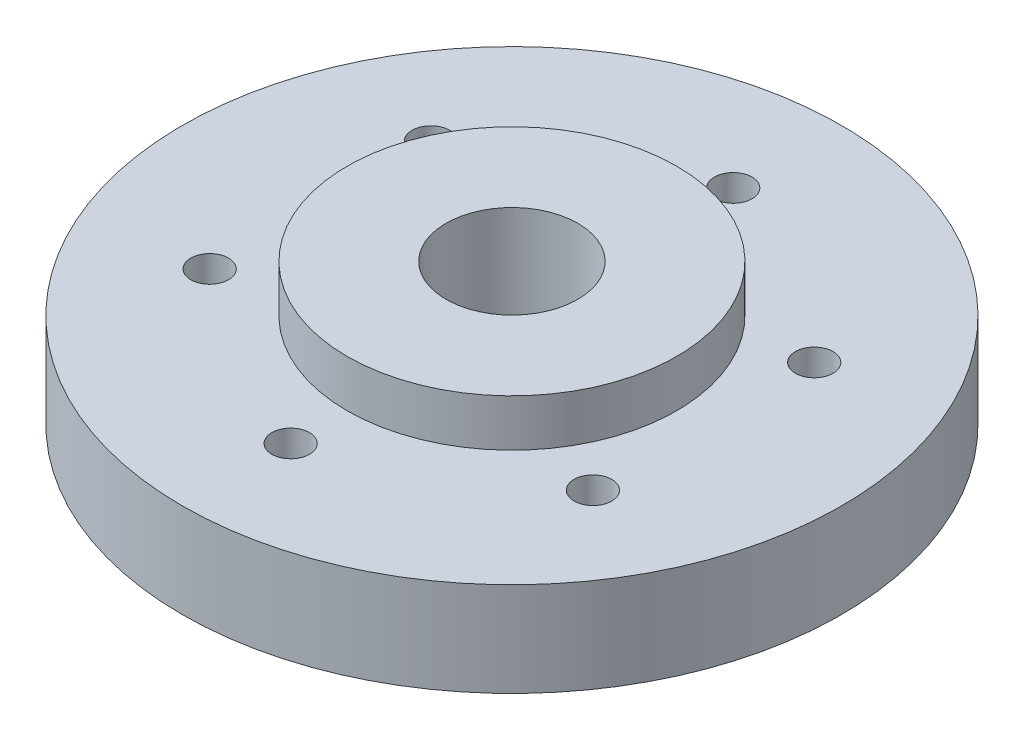
SolidWorks part; units mm, degrees
ref_plane "Front Plane" through (0, 0, 0) normal (0, 0, 1) x (1, 0, 0)
ref_plane "Top Plane" through (0, 0, 0) normal (0, 1, 0) x (1, 0, 0)
ref_plane "Right Plane" through (0, 0, 0) normal (1, 0, 0) x (0, 0, -1)
sketch "Sketch1" plane through (0, 0, 0) normal (0, 1, 0) x (1, 0, 0)
  circle A0 centre (0, 0) radius 35
  dimension "D1" = 70
extrude "Boss-Extrude1" add sketch "Sketch1" along normal blind 15
sketch "Sketch3" plane through (0, 0, 0) normal (0, -1, 0) x (1, 0, 0)
  circle A0 centre (0, 0) radius 15.75
  dimension "D1" = 31.5
extrude "Cut-Extrude1" cut sketch "Sketch3" against normal blind 5
sketch "Sketch4" plane through (0, 5, 0) normal (0, -1, 0) x (1, 0, 0)
  circle A0 centre (0, 0) radius 7
  dimension "D1" = 14
extrude "Cut-Extrude2" cut sketch "Sketch4" against normal through all
sketch "Sketch5" plane through (0, 15, 0) normal (0, 1, 0) x (1, 0, 0)
  circle A0 centre (0, 0) radius 17.5
  circle A1 centre (0, 0) radius 35 construction
  circle A2 centre (0, 0) radius 35
  dimension "D1" = 35
extrude "Cut-Extrude3" cut sketch "Sketch5" against normal blind 5
sketch "Sketch6" plane through (0, 10, 0) normal (0, 1, 0) x (1, 0, 0)
  circle A0 centre (0, 0) radius 23.5 construction
  circle A1 centre (0, 23.5) radius 2
  circle A2 centre (20.3516, 11.75) radius 2
  circle A3 centre (20.3516, -11.75) radius 2
  circle A4 centre (0, -23.5) radius 2
  circle A5 centre (-20.3516, -11.75) radius 2
  circle A6 centre (-20.3516, 11.75) radius 2
  point P17 (0, 0)
  dimension "D1" = 47
  dimension "D2" = 4
  dimension "D3" = 6
extrude "Cut-Extrude4" cut sketch "Sketch6" against normal through all
sketch "Sketch7" plane through (0, 0, 0) normal (0, -1, 0) x (1, 0, 0)
  circle A0 centre (20.3516, 11.75) radius 2 construction
  circle A1 centre (20.3516, -11.75) radius 2 construction
  circle A2 centre (0, -23.5) radius 2 construction
  circle A3 centre (-20.3516, -11.75) radius 2 construction
  circle A4 centre (-20.3516, 11.75) radius 2 construction
  circle A5 centre (0, 23.5) radius 2 construction
  circle A6 centre (20.3516, 11.75) radius 2
  circle A7 centre (20.3516, -11.75) radius 2
  circle A8 centre (0, -23.5) radius 2
  circle A9 centre (-20.3516, -11.75) radius 2
  circle A10 centre (-20.3516, 11.75) radius 2
  circle A11 centre (0, 23.5) radius 2
  circle A12 centre (0, 23.5) radius 5
  circle A13 centre (20.3516, 11.75) radius 5
  circle A14 centre (20.3516, -11.75) radius 5
  circle A15 centre (0, -23.5) radius 5
  circle A16 centre (-20.3516, -11.75) radius 5
  circle A17 centre (-20.3516, 11.75) radius 5
  point P31 (0, 0)
  dimension "D1" = 10
  dimension "D2" = 6
extrude "Cut-Extrude5" cut sketch "Sketch7" against normal blind 5
